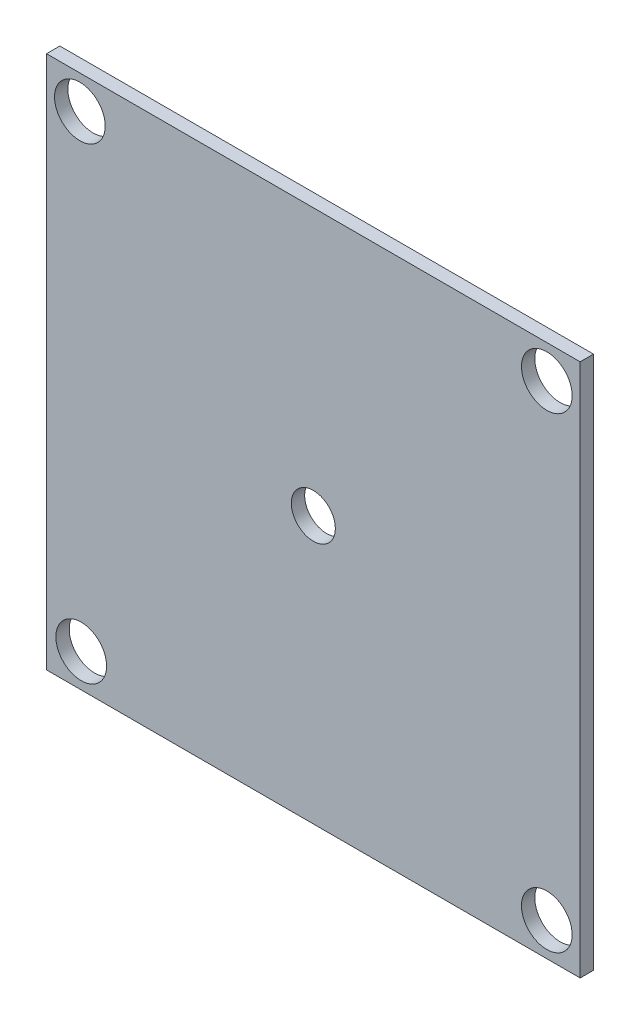
SolidWorks part; units mm, degrees
ref_plane "Front Plane" through (0, 0, 0) normal (0, 0, 1) x (1, 0, 0)
ref_plane "Top Plane" through (0, 0, 0) normal (0, 1, 0) x (1, 0, 0)
ref_plane "Right Plane" through (0, 0, 0) normal (1, 0, 0) x (0, 0, -1)
sketch "Sketch1" plane through (0, 0, 0) normal (0, 0, 1) x (1, 0, 0)
  line L1 (50.8, -50.8) -> (-50.8, -50.8)
  line L2 (50.8, -50.8) -> (50.8, 50.8)
  line L3 (50.8, 50.8) -> (-50.8, 50.8)
  line L4 (-50.8, -50.8) -> (-50.8, 50.8)
  line L5 (50.8, -50.8) -> (-50.8, 50.8) construction
  line L6 (50.8, 50.8) -> (-50.8, -50.8) construction
  point P0 (0, 0)
  dimension "D1" = 101.6
  dimension "D2" = 101.6
extrude "Boss-Extrude1" add sketch "Sketch1" along normal blind 2.54
sketch "Sketch2" plane through (0, 0, 2.54) normal (0, 0, 1) x (1, 0, 0)
  line L0 (0, 50.8) -> (0, -50.8) construction
  line L1 (50.8, 50.8) -> (-50.8, 50.8) construction
  line L2 (-50.8, -50.8) -> (50.8, -50.8) construction
  line L3 (-50.8, 50.8) -> (-50.8, -50.8) construction
  line L4 (50.8, -50.8) -> (50.8, 50.8) construction
  circle A0 centre (-44.45, 44.45) radius 4.826
  circle A1 centre (44.45, 44.45) radius 4.826
  circle A2 centre (44.45, -44.45) radius 4.826
  circle A3 centre (-44.1908, -44.45) radius 4.826
  point P12 (-44.1908, 44.08)
  point P15 (43.9693, 44.08)
  point P16 (0, 0)
  point P17 (42.1972, -42.751)
  point P18 (0, 0)
  point P19 (-44.1908, -42.751)
  dimension "D1" = 9.652
  dimension "D2" = 9.652
  dimension "D3" = 9.652
  dimension "D4" = 9.652
  dimension "D5" = 6.35
  dimension "D6" = 6.35
  dimension "D7" = 6.35
  dimension "D8" = 6.6092
  dimension "D9" = 6.35
  dimension "D10" = 6.35
  dimension "D11" = 6.35
  dimension "D12" = 6.35
sketch "Sketch3" plane through (0, 0, 2.54) normal (0, 0, 1) x (1, 0, 0)
  circle A0 centre (0, 0) radius 4.191
  dimension "D1" = 8.382
extrude "Cut-Extrude2" cut sketch "Sketch3" against normal blind 2.54
extrude "Cut-Extrude3" cut sketch "Sketch2" against normal blind 2.54 contours A3 | A0 | A1 | A2
